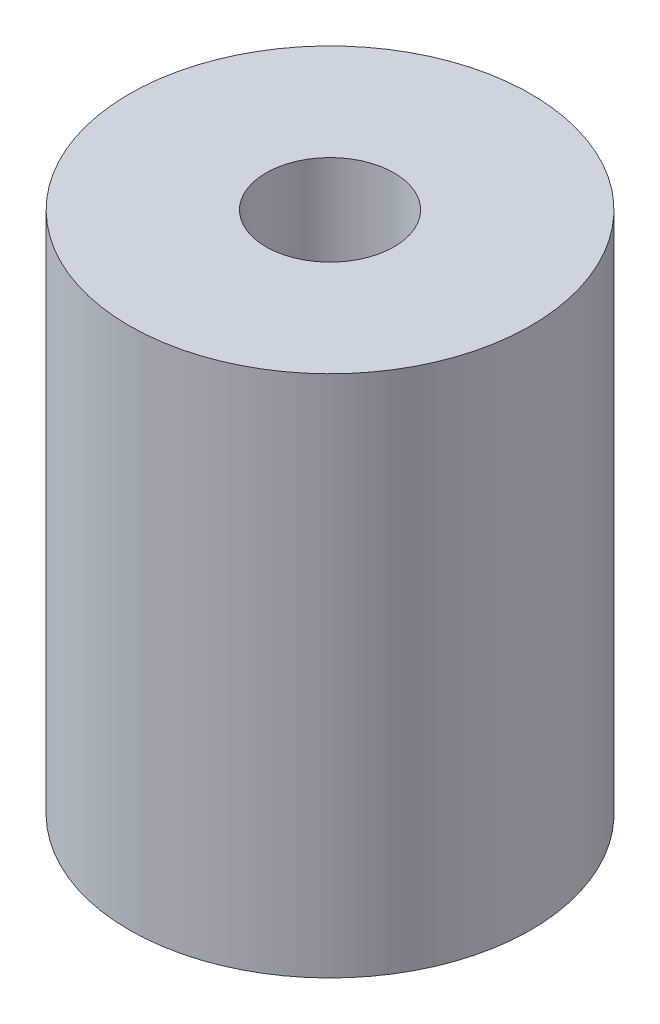
SolidWorks part; units mm, degrees
ref_plane "Front Plane" through (0, 0, 0) normal (0, 0, 1) x (1, 0, 0)
ref_plane "Top Plane" through (0, 0, 0) normal (0, 1, 0) x (1, 0, 0)
ref_plane "Right Plane" through (0, 0, 0) normal (1, 0, 0) x (0, 0, -1)
sketch "Sketch2" plane through (0, 0, 0) normal (0, 1, 0) x (1, 0, 0)
  circle A0 centre (0, 0) radius 9.4
  dimension "D1" = 18.8
extrude "Boss-Extrude1" add sketch "Sketch2" along normal blind 24.5
sketch "Sketch3" plane through (0, 24.5, 0) normal (0, 1, 0) x (1, 0, 0)
  circle A0 centre (0, 0) radius 3
  dimension "D1" = 6
extrude "Cut-Extrude1" cut sketch "Sketch3" against normal blind 7.9
sketch "Sketch4" plane through (0, 0, 0) normal (0, -1, 0) x (1, 0, 0)
  circle A0 centre (0, 0) radius 3.175
  dimension "D1" = 6.35
extrude "Cut-Extrude2" cut sketch "Sketch4" against normal blind 16.6
